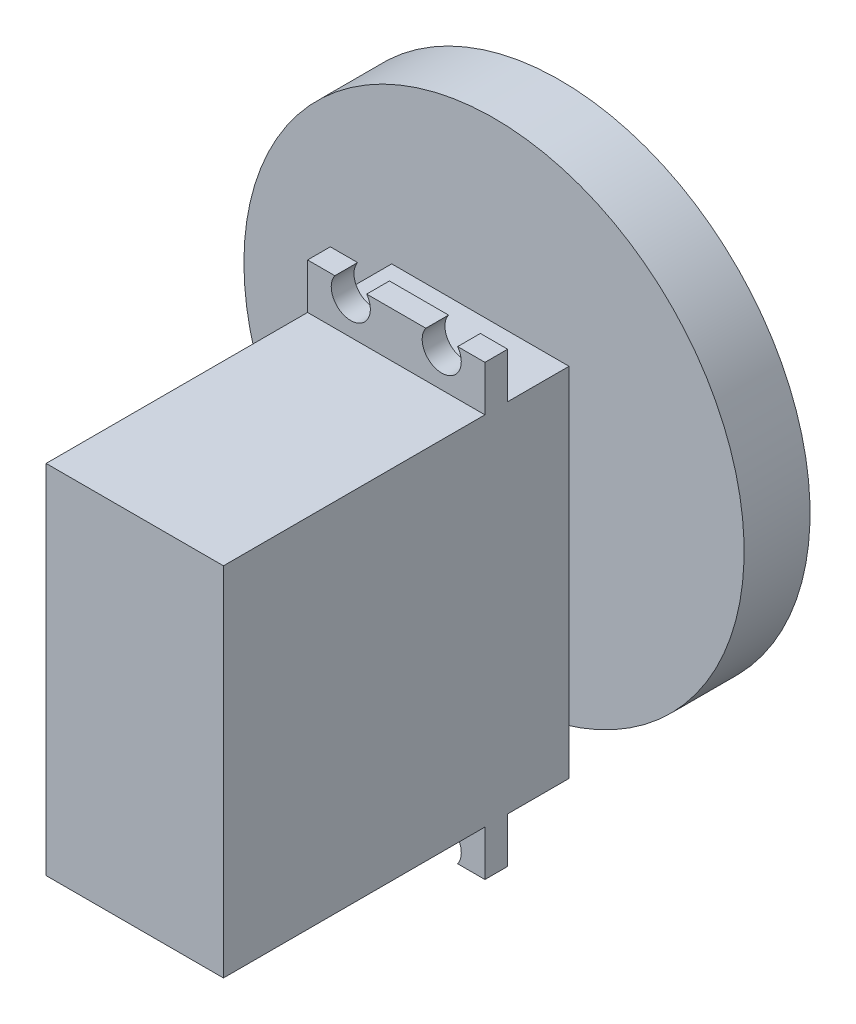
SolidWorks part; units mm, degrees
material "ABS"
ref_plane "Front Plane" through (0, 0, 0) normal (0, 0, 1) x (1, 0, 0)
ref_plane "Top Plane" through (0, 0, 0) normal (0, 1, 0) x (1, 0, 0)
ref_plane "Right Plane" through (0, 0, 0) normal (1, 0, 0) x (0, 0, -1)
sketch "Sketch1" plane through (0, 0, 0) normal (0, 0, 1) x (1, 0, 0)
  line L1 (0, 0) -> (19.812, 0)
  line L2 (0, 0) -> (0, 39.878)
  line L3 (0, 39.878) -> (19.812, 39.878)
  line L4 (19.812, 0) -> (19.812, 39.878)
  dimension "D1" = 19.812
  dimension "D2" = 39.878
extrude "Boss-Extrude1" add sketch "Sketch1" along normal blind 29.21
sketch "Sketch2" plane through (0, 0, 0) normal (0, 0, -1) x (-1, 0, 0)
  line L0 (0, 39.878) -> (0, 0) construction
  line L1 (0, -5.08) -> (-3.0487, -5.08)
  line L2 (0, -5.08) -> (0, 44.958)
  line L3 (0, 44.958) -> (-3.0487, 44.958)
  line L4 (-19.812, -5.08) -> (-19.812, 44.958)
  line L5 (-19.812, 0) -> (-19.812, 39.878) construction
  line L6 (-19.812, 39.878) -> (0, 39.878) construction
  line L7 (0, 0) -> (-19.812, 0) construction
  line L8 (-4.826, 43.688) -> (-14.986, 43.688) construction
  line L9 (-6.6033, 44.958) -> (-13.2087, 44.958)
  line L10 (-16.7633, 44.958) -> (-19.812, 44.958)
  line L11 (-4.826, -3.81) -> (-14.986, -3.81) construction
  line L12 (-6.6033, -5.08) -> (-13.2087, -5.08)
  line L13 (-16.7633, -5.08) -> (-19.812, -5.08)
  arc A0 (-6.6033, 44.958) -> (-3.0487, 44.958) centre (-4.826, 43.688) ccw
  arc A1 (-16.7633, 44.958) -> (-13.2087, 44.958) centre (-14.986, 43.688) ccw
  arc A2 (-3.0487, -5.08) -> (-6.6033, -5.08) centre (-4.826, -3.81) ccw
  arc A3 (-13.2087, -5.08) -> (-16.7633, -5.08) centre (-14.986, -3.81) ccw
  point P12 (-9.906, 39.878)
  point P15 (-9.906, 43.688)
  point P22 (-9.906, -3.81)
  point P23 (-9.906, 0)
  dimension "D5" = 4.3688
  dimension "D8" = 4.3688
  dimension "D1" = 5.08
  dimension "D2" = 5.08
  dimension "D3" = 3.81
  dimension "D4" = 10.16
  dimension "D6" = 3.81
  dimension "D7" = 10.16
  dimension "D9" = 47.498
extrude "Boss-Extrude2" add sketch "Sketch2" along normal blind 2.54
sketch "Sketch3" plane through (0, 0, -2.54) normal (0, 0, -1) x (-1, 0, 0)
  line L4 (0, 0) -> (0, 39.878)
  line L5 (-19.812, 0) -> (0, 0)
  line L6 (-19.812, 39.878) -> (-19.812, 0)
  line L7 (0, 39.878) -> (-19.812, 39.878)
  line L8 (0, 0) -> (0, 39.878)
  line L9 (-19.812, 0) -> (0, 0)
  line L10 (-19.812, 39.878) -> (-19.812, 0)
  line L11 (0, 39.878) -> (-19.812, 39.878)
  dimension "D1" = 0
extrude "Boss-Extrude3" add sketch "Sketch3" along normal blind 6.858
sketch "Sketch4" plane through (0, 0, -9.398) normal (0, 0, -1) x (-1, 0, 0)
  line L0 (0, 39.878) -> (-19.812, 39.878) construction
  circle A0 centre (-9.906, 30.226) radius 6.35
  point P4 (-9.906, 39.878)
  dimension "D1" = 12.7
  dimension "D2" = 9.652
extrude "Boss-Extrude4" add sketch "Sketch4" along normal blind 1.524
sketch "Sketch9" plane through (0, 0, -10.922) normal (0, 0, -1) x (-1, 0, 0)
  circle A0 centre (-9.906, 30.226) radius 1.905
  circle A1 centre (-9.906, 30.226) radius 6.35 construction
  circle A2 centre (-9.906, 30.226) radius 27.94
  dimension "D1" = 3.81
  dimension "D2" = 55.88
extrude "Boss-Extrude6" add sketch "Sketch9" along normal blind 7.366
